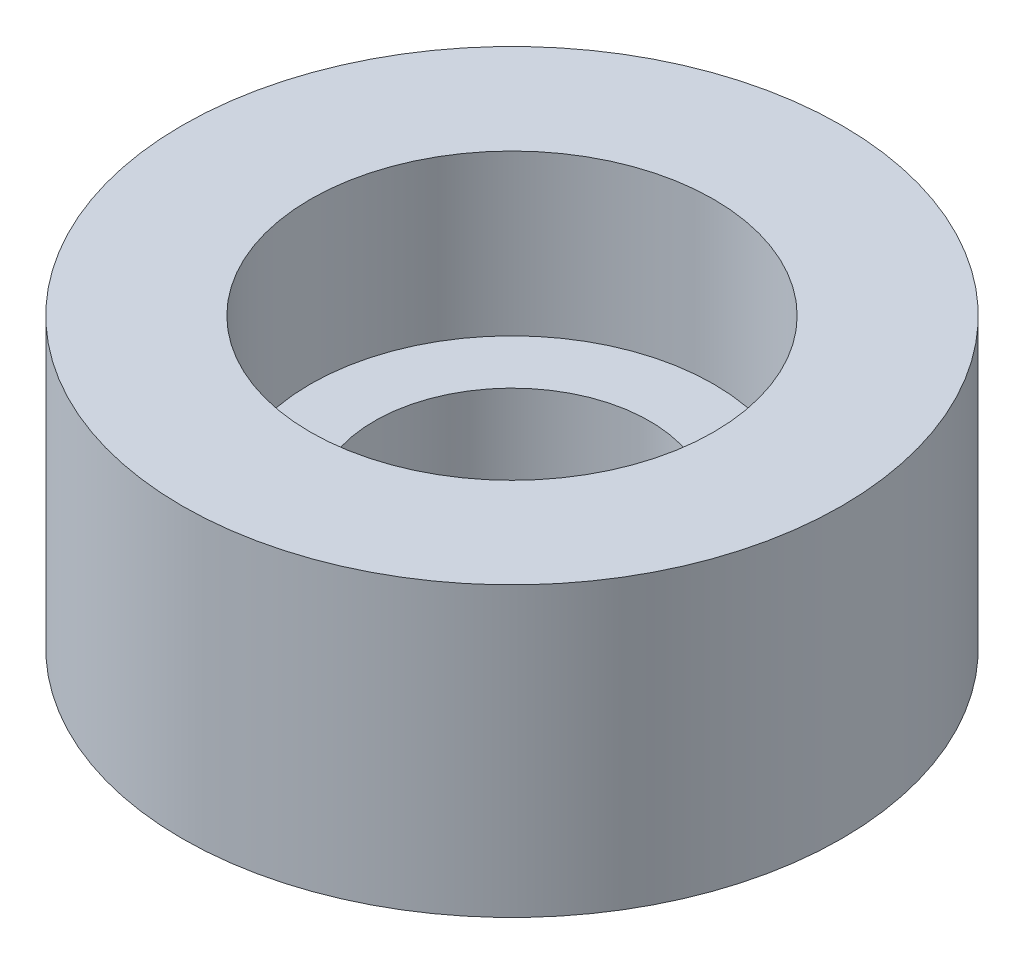
SolidWorks part; units mm, degrees
material "ABS"
ref_plane "Front Plane" through (0, 0, 0) normal (0, 0, 1) x (1, 0, 0)
ref_plane "Top Plane" through (0, 0, 0) normal (0, 1, 0) x (1, 0, 0)
ref_plane "Right Plane" through (0, 0, 0) normal (1, 0, 0) x (0, 0, -1)
sketch "Sketch1" plane through (0, 0, 0) normal (0, 1, 0) x (1, 0, 0)
  circle A0 centre (0, 0) radius 3.15
  dimension "D1" = 6.3
extrude "Extrude-Thin1" add sketch "Sketch1" along normal blind 4.5 thin
sketch "Sketch2" plane through (0, 0, 0) normal (0, 1, 0) x (1, 0, 0)
  circle A1 centre (0, 0) radius 2.15
  circle A2 centre (0, 0) radius 3.15 construction
  circle A3 centre (0, 0) radius 3.15
  dimension "D1" = 4.3
extrude "Boss-Extrude1" add sketch "Sketch2" along normal blind 2
